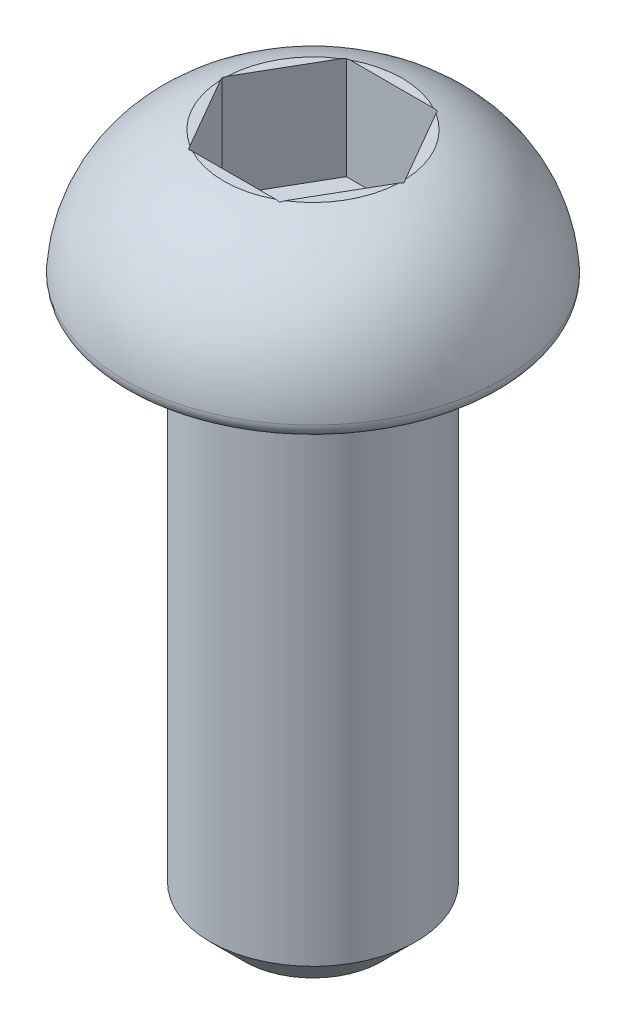
SolidWorks part; units mm, degrees
ref_plane "前视" through (0, 0, 0) normal (0, 0, 1) x (1, 0, 0)
ref_plane "上视" through (0, 0, 0) normal (0, 1, 0) x (1, 0, 0)
ref_plane "右视" through (0, 0, 0) normal (1, 0, 0) x (0, 0, -1)
sketch "草图1" plane through (0, 0, 0) normal (0, 0, 1) x (1, 0, 0)
  line L0 (0, 0) -> (0, 2)
  line L1 (0, 2) -> (1.3, 2)
  line L2 (0, 0) -> (2.75, 0)
  arc A0 (1.3, 2) -> (2.75, 0) centre (0.7515, 0.0767) cw
  dimension "D4" = 2
  dimension "D1" = 1.3
  dimension "D2" = 2.75
  dimension "D3" = 2
revolve "旋转1" add sketch "草图1" angle 360 about L0
fillet "圆角1" radius 0.2 1 edges at (0, 0, -2.75)
sketch "草图2" plane through (0, 2, 0) normal (0, 1, 0) x (1, 0, 0)
  line L1 (1.3279, 0) -> (0.664, 1.15)
  line L2 (0.664, 1.15) -> (-0.664, 1.15)
  line L3 (-0.664, 1.15) -> (-1.3279, 0)
  line L4 (-1.3279, 0) -> (-0.664, -1.15)
  line L5 (-0.664, -1.15) -> (0.664, -1.15)
  line L6 (0.664, -1.15) -> (1.3279, 0)
  circle A0 centre (0, 0) radius 1.15 construction
  dimension "D1" = 2.3
extrude "切除-拉伸1" cut sketch "草图2" against normal blind 1.5
sketch "草图3" plane through (0, 0, 0) normal (0, -1, 0) x (1, 0, 0)
  circle A0 centre (0, 0) radius 1.5
  dimension "D1" = 3
extrude "凸台-拉伸1" add sketch "草图3" along normal blind 8
chamfer "倒角1" distance 0.5 angle 45 1 edges at (0, -8, -1.5)
